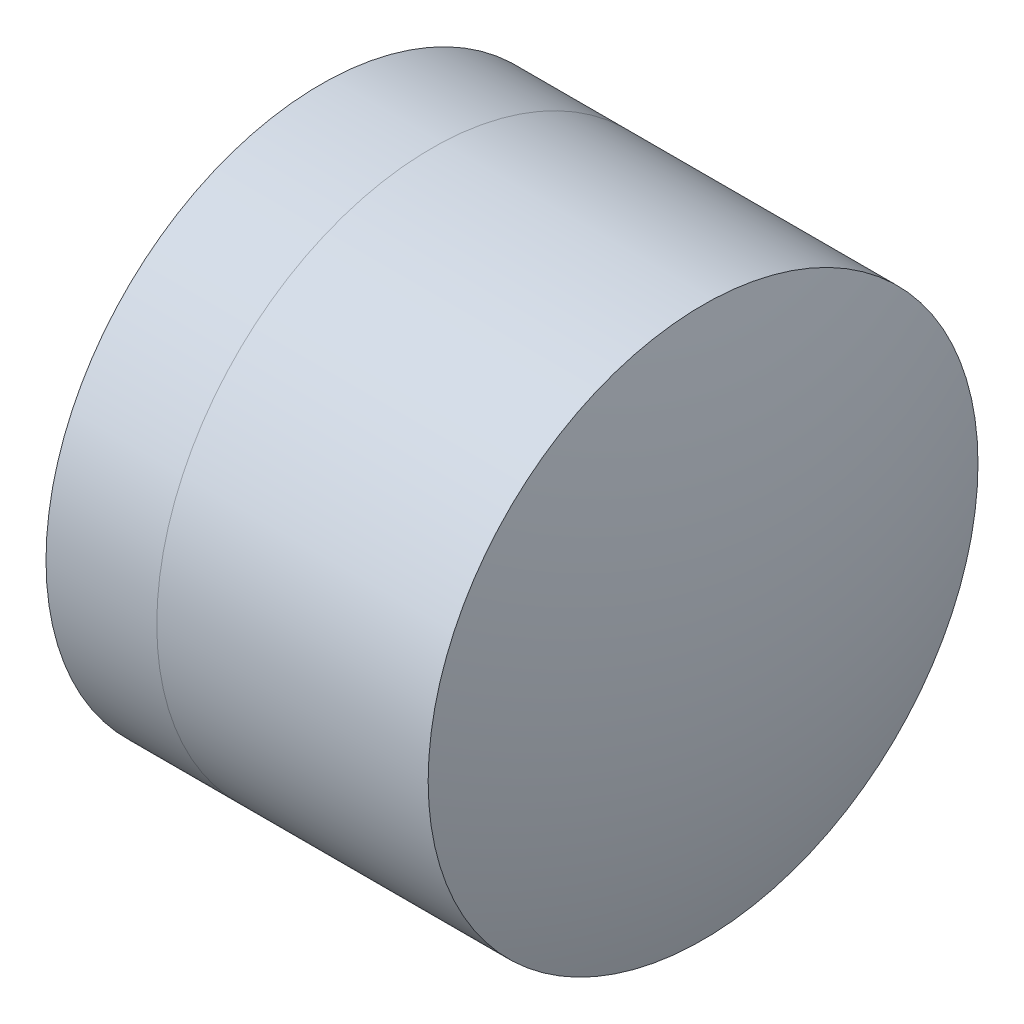
SolidWorks part; units mm, degrees
ref_plane "前视基准面" through (0, 0, 0) normal (0, 0, 1) x (1, 0, 0)
ref_plane "上视基准面" through (0, 0, 0) normal (0, 1, 0) x (1, 0, 0)
ref_plane "右视基准面" through (0, 0, 0) normal (1, 0, 0) x (0, 0, -1)
sketch "草图1" plane through (0, 0, 0) normal (0, 1, 0) x (1, 0, 0)
  line L0 (-0.8161, 0) -> (3.5052, 0) construction
  line L1 (1.1334, -2) -> (1.9393, -2)
  line L2 (1.1334, 2) -> (1.9393, 2)
  arc A0 (1.9393, -2) -> (1.9393, 2) centre (0.178, 0) ccw
  arc A1 (1.1334, 2) -> (1.1334, -2) centre (4.966, 0) ccw
  point P10 (0.643, 0)
  point P11 (2.843, 0)
  dimension "D3" = 4.323
  dimension "D4" = 2.665
  dimension "D1" = 2
  dimension "D2" = 2
  dimension "D5" = 2.2
revolve "旋转1" add sketch "草图1" angle 360 about L0
sketch "草图2" plane through (0, 0, 0) normal (0, 1, 0) x (1, 0, 0)
  line L0 (-0.5519, 0) -> (4.9438, 0) construction
  line L2 (1.9393, 2) -> (3.9134, 2)
  line L3 (1.9393, -2) -> (3.9134, -2)
  arc A0 (3.9134, -2) -> (3.9134, 2) centre (-2.186, 0) ccw
  arc A1 (1.9393, -2) -> (1.9393, 2) centre (0.178, 0) ccw construction
  arc A2 (1.9393, -2) -> (1.9393, 2) centre (0.178, 0) ccw
  point P4 (2.843, 0)
  point P8 (4.233, 0)
  dimension "D1" = 6.419
  dimension "D2" = 1.39
revolve "旋转3" add sketch "草图2" angle 360 about L0
